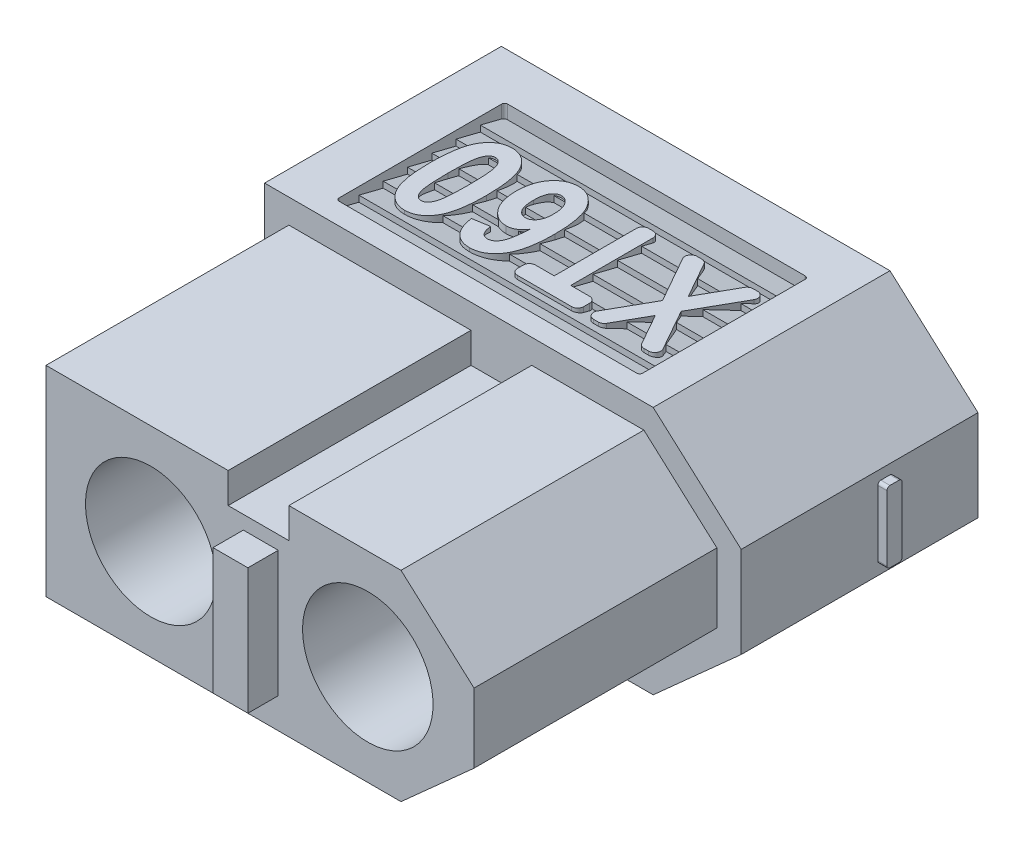
SolidWorks part; units mm, degrees
material "Náilon 101"
ref_plane "Plano frontal" through (0, 0, 0) normal (0, 0, 1) x (1, 0, 0)
ref_plane "Plano superior" through (0, 0, 0) normal (0, 1, 0) x (1, 0, 0)
ref_plane "Plano direito" through (0, 0, 0) normal (1, 0, 0) x (0, 0, -1)
sketch "Esboço1" plane through (0, 0, 0) normal (0, 0, 1) x (1, 0, 0)
  line L0 (0, 0) -> (12.8, 0)
  line L1 (12.8, 0) -> (15.7, 2.6)
  line L2 (15.7, 2.6) -> (15.7, 5.6)
  line L3 (15.7, 5.6) -> (12.8, 8.2)
  line L4 (12.8, 8.2) -> (0, 8.2)
  line L5 (0, 8.2) -> (0, 0)
  dimension "D1" = 12.8
  dimension "D2" = 3
  dimension "D3" = 15.7
  dimension "D4" = 8.2
extrude "Ressalto-extrusão1" add sketch "Esboço1" along normal blind 15.8
sketch "Esboço2" plane through (0, 0, 15.8) normal (0, 0, 1) x (1, 0, 0)
  line L0 (0.8, 7.4) -> (0.8, 0.8)
  line L1 (0.8, 0.8) -> (12.4939, 0.8)
  line L2 (12.4939, 0.8) -> (14.9, 2.9572)
  line L3 (14.9, 2.9572) -> (14.9, 5.2428)
  line L4 (14.9, 5.2428) -> (12.4939, 7.4)
  line L5 (12.4939, 7.4) -> (8.8, 7.4)
  line L6 (0, 8.2) -> (0, 0)
  line L7 (0, 0) -> (12.8, 0)
  line L8 (12.8, 0) -> (15.7, 2.6)
  line L9 (15.7, 2.6) -> (15.7, 5.6)
  line L10 (15.7, 5.6) -> (12.8, 8.2)
  line L11 (12.8, 8.2) -> (0, 8.2)
  line L12 (0, 8.2) -> (0, 0)
  line L13 (0, 0) -> (12.8, 0)
  line L14 (12.8, 0) -> (15.7, 2.6)
  line L15 (15.7, 2.6) -> (15.7, 5.6)
  line L16 (15.7, 5.6) -> (12.8, 8.2)
  line L17 (12.8, 8.2) -> (0, 8.2)
  line L18 (6.8, 7.4) -> (0.8, 7.4)
  line L20 (6.8, 7.4) -> (6.8, 6.4)
  line L21 (6.8, 6.4) -> (8.8, 6.4)
  line L22 (8.8, 7.4) -> (8.8, 6.4)
  line L23 (12.4939, 7.4) -> (0.8, 7.4) construction
  dimension "D3" = 2
  dimension "D4" = 6
  dimension "D5" = 1
  dimension "D1" = 0
  dimension "D2" = 0.8
extrude "Corte-extrusão1" cut sketch "Esboço2" against normal blind 8
sketch "Esboço5" plane through (0, 0, 0) normal (0, 0, -1) x (-1, 0, 0)
  line L0 (-15.7, 2.6) -> (-15.7, 5.6) construction
  line L3 (0, 8.2) -> (0, 0) construction
  circle A0 centre (-11.4, 4.1) radius 3
  circle A1 centre (-4.25, 4.1) radius 3
  point P6 (-15.7, 4.1)
  point P9 (-15.7, 4.1)
  dimension "D1" = 6
  dimension "D3" = 4.25
  dimension "D2" = 4.3
extrude "Corte-extrusão3" cut sketch "Esboço5" against normal blind 2
sketch "Esboço6" plane through (0, 0, 2) normal (0, 0, -1) x (-1, 0, 0)
  circle A0 centre (-11.4, 4.1) radius 2.15
  circle A1 centre (-11.4, 4.1) radius 3 construction
  circle A2 centre (-4.25, 4.1) radius 2.15
  dimension "D1" = 4.3
  dimension "D2" = 2.85
extrude "Corte-extrusão4" cut sketch "Esboço6" against normal through all
sketch "Esboço7" plane through (0, 0, 0) normal (-1, 0, 0) x (0, 0, 1)
  line L0 (2.8, 4.35) -> (2.05, 4.35)
  line L1 (4.25, 4.35) -> (3.5, 4.35)
  line L2 (4.35, 4.25) -> (4.35, 3.95)
  line L3 (4.25, 3.85) -> (3.5, 3.85)
  line L4 (1.95, 4.25) -> (1.95, 3.95)
  line L5 (3.3, 5.3) -> (3, 5.3)
  line L6 (3.4, 5.2) -> (3.4, 4.45)
  line L7 (3.3, 2.9) -> (3, 2.9)
  line L8 (2.9, 5.2) -> (2.9, 4.45)
  line L9 (2.8, 3.85) -> (2.05, 3.85)
  line L10 (3.4, 3.75) -> (3.4, 3)
  line L11 (2.9, 3.75) -> (2.9, 3)
  line L12 (0, 8.2) -> (0, 0) construction
  arc A0 (3, 2.9) -> (2.9, 3) centre (3, 3) cw
  arc A1 (3.3, 5.3) -> (3.4, 5.2) centre (3.3, 5.2) cw
  arc A2 (3, 5.3) -> (2.9, 5.2) centre (3, 5.2) ccw
  arc A3 (2.05, 4.35) -> (1.95, 4.25) centre (2.05, 4.25) ccw
  arc A4 (2.05, 3.85) -> (1.95, 3.95) centre (2.05, 3.95) cw
  arc A5 (2.8, 3.85) -> (2.9, 3.75) centre (2.8, 3.75) cw
  arc A6 (2.8, 4.35) -> (2.9, 4.45) centre (2.8, 4.45) ccw
  arc A7 (3.5, 3.85) -> (3.4, 3.75) centre (3.5, 3.75) ccw
  arc A8 (3.4, 3) -> (3.3, 2.9) centre (3.3, 3) cw
  arc A9 (4.35, 3.95) -> (4.25, 3.85) centre (4.25, 3.95) cw
  arc A10 (4.25, 4.35) -> (4.35, 4.25) centre (4.25, 4.25) cw
  arc A11 (3.5, 4.35) -> (3.4, 4.45) centre (3.5, 4.45) cw
  point P12 (1.95, 4.1)
  point P15 (0, 4.1)
  point P28 (2.9, 3.85)
  point P33 (3.4, 3.85)
  point P38 (4.35, 3.85)
  point P41 (4.35, 4.35)
  dimension "D4" = 0.1
  dimension "D1" = 2.4
  dimension "D2" = 0.5
  dimension "D3" = 4.35
extrude "Ressalto-extrusão3" add sketch "Esboço7" along normal blind 0.3
sketch "Esboço8" plane through (15.7, 0, 0) normal (1, 0, 0) x (0, 0, -1)
  line L0 (0, 2.6) -> (0, 5.6) construction
  line L1 (-3.2, 2.925) -> (-2.9, 2.925)
  line L2 (-3.3, 3.025) -> (-3.3, 5.175)
  line L3 (-3.2, 5.275) -> (-2.9, 5.275)
  line L4 (-2.8, 3.025) -> (-2.8, 5.175)
  arc A0 (-3.3, 5.175) -> (-3.2, 5.275) centre (-3.2, 5.175) cw
  arc A1 (-2.9, 5.275) -> (-2.8, 5.175) centre (-2.9, 5.175) cw
  arc A2 (-3.2, 2.925) -> (-3.3, 3.025) centre (-3.2, 3.025) cw
  arc A3 (-2.9, 2.925) -> (-2.8, 3.025) centre (-2.9, 3.025) ccw
  point P4 (-2.8, 4.1)
  point P7 (0, 4.1)
  point P10 (-3.3, 5.275)
  point P13 (-2.8, 5.275)
  point P18 (-2.8, 2.925)
  dimension "D4" = 0.1
  dimension "D1" = 2.35
  dimension "D2" = 0.5
  dimension "D3" = 3.3
extrude "Ressalto-extrusão4" add sketch "Esboço8" along normal blind 0.3
sketch "Esboço9" plane through (0, 0, 0) normal (0, -1, 0) x (1, 0, 0)
  line L0 (12.8, 7.8) -> (12.8, 0) construction
  line L1 (1.75, 7.0931) -> (11.55, 7.0931)
  line L2 (1.65, 6.9931) -> (1.65, 1.6431)
  line L3 (1.75, 1.5431) -> (11.55, 1.5431)
  line L4 (11.65, 6.9931) -> (11.65, 1.6431)
  arc A0 (1.65, 1.6431) -> (1.75, 1.5431) centre (1.75, 1.6431) ccw
  arc A1 (11.55, 1.5431) -> (11.65, 1.6431) centre (11.55, 1.6431) ccw
  arc A2 (11.55, 7.0931) -> (11.65, 6.9931) centre (11.55, 6.9931) cw
  arc A3 (1.75, 7.0931) -> (1.65, 6.9931) centre (1.75, 6.9931) ccw
  dimension "D1" = 0.1
  dimension "D2" = 1.15
  dimension "D3" = 10
  dimension "D4" = 5.55
extrude "Corte-extrusão5" cut sketch "Esboço9" against normal blind 0.75
sketch "Esboço10" plane through (1.65, 0, 0) normal (1, 0, 0) x (0, 0, -1)
  line L0 (-6.9931, 0.75) -> (-1.6431, 0.75) construction
  line L1 (-1.5431, 0.75) -> (-1.5431, 0) construction
  line L2 (-3.1431, 0.25) -> (-2.3431, 0.45)
  line L3 (-2.3431, 0.45) -> (-2.3431, 0.25)
  line L5 (-3.1431, 0.45) -> (-3.1431, 0.25)
  line L6 (-2.3431, 0.45) -> (-2.3431, 0.25)
  line L7 (-3.9431, 0.25) -> (-3.1431, 0.45)
  line L8 (-3.9431, 0.45) -> (-3.9431, 0.25)
  line L9 (-4.7431, 0.25) -> (-3.9431, 0.45)
  line L10 (-4.7431, 0.45) -> (-4.7431, 0.25)
  line L11 (-5.5431, 0.25) -> (-4.7431, 0.45)
  line L12 (-5.5431, 0.45) -> (-5.5431, 0.25)
  line L13 (-6.3431, 0.25) -> (-5.5431, 0.45)
  line L14 (-6.3431, 0.45) -> (-6.3431, 0.25)
  line L15 (-7.1431, 0.25) -> (-6.3431, 0.45)
  line L16 (-7.1431, 0.45) -> (-7.1431, 0.25)
  line L17 (-7.1431, 0.45) -> (-7.1431, 0.75)
  line L19 (-2.3431, 0.25) -> (-1.5431, 0.45)
  line L20 (-7.1431, 0.75) -> (-1.5431, 0.75)
  line L21 (-1.5431, 0.45) -> (-1.5431, 0.75)
  line L31 (-2.3431, 0.25) -> (-1.5431, 0.45)
  dimension "D1" = 0.8
  dimension "D2" = 0.2
  dimension "D3" = 0.3
  dimension "D4" = 7
extrude "Ressalto-extrusão7" add sketch "Esboço10" along normal up to surface (10 mm away) up to face at (11.65, 0.375, 4.3181)
ref_plane "Plano1" through (0, 4.1, 0) normal (0, 1, 0) x (1, 0, 0)
mirror "Espelhar1" about plane through (0, 4.1, 0) normal (0, 1, 0) of "Corte-extrusão5", "Ressalto-extrusão7"
ref_plane "Plano2" through (0, 0.5, 0) normal (0, -1, 0) x (-1, 0, 0)
sketch "Esboço11" plane through (0, 0.5, 0) normal (0, -1, 0) x (-1, 0, 0)
  line L0 (-11.65, -5.5431) -> (-1.65, -5.5431) construction
  line L1 (-2.5942, -5.5431) -> (-2.8167, -5.5431)
  line L2 (-2.4442, -5.6931) -> (-2.4442, -5.9931)
  line L3 (-2.5942, -6.1431) -> (-4.2856, -6.1431)
  line L4 (-4.4356, -5.6931) -> (-4.4356, -5.9931)
  line L5 (-2.9644, -5.3671) -> (-2.4752, -2.5928)
  line L6 (-2.6229, -2.4167) -> (-2.9229, -2.4167)
  line L7 (-3.0707, -2.5407) -> (-3.5782, -5.4192)
  line L8 (-7.3128, -6.1431) -> (-5.9872, -6.1431)
  line L9 (-5.8573, -6.0681) -> (-5.8287, -6.0186)
  line L10 (-5.5911, -5.3659) -> (-5.1507, -2.8681)
  line L11 (-5.6643, -2.4167) -> (-6.7472, -2.4167)
  line L12 (-6.8771, -2.4917) -> (-7.2464, -3.1314)
  line L13 (-7.2611, -3.163) -> (-7.4867, -3.7828)
  line L14 (-7.4957, -3.8165) -> (-7.6002, -4.4092)
  line L15 (-7.4525, -4.5852) -> (-6.8146, -4.5852)
  line L16 (-6.6646, -4.4352) -> (-6.6646, -4.1352)
  line L17 (-6.9804, -3.6253) -> (-6.8543, -3.899)
  line L20 (-6.6242, -3.0167) -> (-5.9053, -3.0167)
  line L21 (-5.8069, -3.1341) -> (-6.2098, -5.4192)
  line L22 (-6.9749, -3.4469) -> (-6.8004, -3.1221)
  line L23 (-6.3575, -5.5431) -> (-7.0764, -5.5431)
  line L24 (-7.1749, -5.4258) -> (-7.1512, -5.2917)
  line L25 (-4.4356, -6.1431) -> (-5.9006, -6.1431) construction
  line L26 (-7.2989, -5.1157) -> (-7.599, -5.1157)
  line L27 (-7.7467, -5.2396) -> (-7.8264, -5.6918)
  line L28 (-7.7689, -5.8377) -> (-7.403, -6.113)
  line L29 (-8.9766, -6.1431) -> (-9.2766, -6.1431)
  line L30 (-9.4266, -5.9918) -> (-9.4198, -5.2132)
  line L31 (-9.5094, -5.1823) -> (-10.2035, -6.0846)
  line L32 (-10.3224, -6.1431) -> (-10.6224, -6.1431)
  line L33 (-10.7413, -5.9017) -> (-9.4154, -4.178)
  line L34 (-9.4154, -4.178) -> (-9.1267, -2.5407)
  line L35 (-8.979, -2.4167) -> (-8.679, -2.4167)
  line L36 (-8.5313, -2.5928) -> (-8.8108, -4.178)
  line L37 (-8.8108, -4.178) -> (-8.8266, -5.9944)
  line L38 (-3.7259, -5.5431) -> (-4.2856, -5.5431)
  line L39 (-5.2082, -2.7221) -> (-5.5741, -2.4469)
  line L40 (-7.3629, -6.1431) -> (-8.8279, -6.1431) construction
  line L41 (-11.55, -7.0931) -> (-1.75, -7.0931) construction
  arc A0 (-6.2098, -5.4192) -> (-6.3575, -5.5431) centre (-6.3575, -5.3931) cw
  arc A1 (-7.2464, -3.1314) -> (-7.2611, -3.163) centre (-7.0732, -3.2314) ccw
  arc A2 (-7.4957, -3.8165) -> (-7.4867, -3.7828) centre (-7.2988, -3.8512) cw
  arc A3 (-6.8543, -3.899) -> (-6.7538, -3.9981) centre (-6.6727, -3.8153) ccw
  arc A4 (-6.6646, -4.1352) -> (-6.7538, -3.9981) centre (-6.8146, -4.1352) ccw
  arc A5 (-6.8146, -4.5852) -> (-6.6646, -4.4352) centre (-6.8146, -4.4352) ccw
  arc A6 (-7.6002, -4.4092) -> (-7.4525, -4.5852) centre (-7.4525, -4.4352) ccw
  arc A7 (-7.1512, -5.2917) -> (-7.2989, -5.1157) centre (-7.2989, -5.2657) ccw
  arc A8 (-7.599, -5.1157) -> (-7.7467, -5.2396) centre (-7.599, -5.2657) ccw
  arc A9 (-10.6224, -6.1431) -> (-10.7413, -5.9017) centre (-10.6224, -5.9931) cw
  arc A10 (-10.2035, -6.0846) -> (-10.3224, -6.1431) centre (-10.3224, -5.9931) cw
  arc A11 (-9.2766, -6.1431) -> (-9.4266, -5.9918) centre (-9.2766, -5.9931) cw
  arc A12 (-8.9766, -6.1431) -> (-8.8266, -5.9944) centre (-8.9766, -5.9931) ccw
  arc A13 (-8.679, -2.4167) -> (-8.5313, -2.5928) centre (-8.679, -2.5667) cw
  arc A14 (-9.1267, -2.5407) -> (-8.979, -2.4167) centre (-8.979, -2.5667) cw
  arc A15 (-2.4752, -2.5928) -> (-2.6229, -2.4167) centre (-2.6229, -2.5667) ccw
  arc A16 (-2.9229, -2.4167) -> (-3.0707, -2.5407) centre (-2.9229, -2.5667) ccw
  arc A17 (-2.9644, -5.3671) -> (-2.8167, -5.5431) centre (-2.8167, -5.3931) ccw
  arc A18 (-3.5782, -5.4192) -> (-3.7259, -5.5431) centre (-3.7259, -5.3931) cw
  arc A19 (-4.2856, -5.5431) -> (-4.4356, -5.6931) centre (-4.2856, -5.6931) ccw
  arc A20 (-4.2856, -6.1431) -> (-4.4356, -5.9931) centre (-4.2856, -5.9931) cw
  arc A21 (-2.5942, -5.5431) -> (-2.4442, -5.6931) centre (-2.5942, -5.6931) cw
  arc A22 (-2.4442, -5.9931) -> (-2.5942, -6.1431) centre (-2.5942, -5.9931) cw
  arc A23 (-7.0764, -5.5431) -> (-7.1749, -5.4258) centre (-7.0764, -5.4431) cw
  arc A24 (-5.9053, -3.0167) -> (-5.8069, -3.1341) centre (-5.9053, -3.1167) cw
  arc A25 (-6.9804, -3.6253) -> (-6.9749, -3.4469) centre (-6.7988, -3.5416) cw
  arc A26 (-5.8287, -6.0186) -> (-5.5911, -5.3659) centre (-7.5607, -5.0186) ccw
  arc A27 (-6.7472, -2.4167) -> (-6.8771, -2.4917) centre (-6.7472, -2.5667) ccw
  arc A28 (-5.5741, -2.4469) -> (-5.6643, -2.4167) centre (-5.6643, -2.5667) ccw
  arc A29 (-5.2082, -2.7221) -> (-5.1507, -2.8681) centre (-5.2984, -2.842) cw
  arc A30 (-5.9872, -6.1431) -> (-5.8573, -6.0681) centre (-5.9872, -5.9931) ccw
  arc A31 (-7.8264, -5.6918) -> (-7.7689, -5.8377) centre (-7.6787, -5.7178) ccw
  arc A32 (-7.3128, -6.1431) -> (-7.403, -6.113) centre (-7.3128, -5.9931) cw
  arc A33 (-9.4198, -5.2132) -> (-9.5094, -5.1823) centre (-9.4698, -5.2128) ccw
  arc A34 (-6.6242, -3.0167) -> (-6.8004, -3.1221) centre (-6.6242, -3.2167) ccw
  point P14 (-6.65, -6.1431)
  point P46 (-6.65, -7.0931)
  point P50 (-6.2316, -5.5431)
  point P67 (-7.7248, -5.1157)
  point P83 (-2.4442, -2.4167)
  point P88 (-2.9954, -5.5431)
  point P91 (-3.6001, -5.5431)
  point P94 (-4.4356, -5.5431)
  point P100 (-2.4442, -5.5431)
  point P103 (-2.4442, -6.1431)
  point P106 (-7.1955, -5.5431)
  point P114 (-5.6524, -5.7132)
  point P119 (-5.6142, -2.4167)
  point P122 (-5.1347, -2.7775)
  dimension "D13" = 0.15
  dimension "D14" = 0.1
  dimension "D16" = 0.15
  dimension "D17" = 0.05
  dimension "D2" = 0.2
  dimension "D4" = 0.2
  dimension "D3" = 0.6
  dimension "D5" = 80
  dimension "D6" = 80
  dimension "D7" = 80
  dimension "D8" = 0.6
  dimension "D9" = 0.6
  dimension "D10" = 60
  dimension "D11" = 0.6
extrude "Ressalto-extrusão8" add sketch "Esboço11" along normal blind 0.3
ref_plane "Plano3" through (0, 7.7, 0) normal (0, 1, 0) x (1, 0, 0)
sketch "Esboço12" plane through (0, 7.7, 0) normal (0, 1, 0) x (1, 0, 0)
  line L0 (11.0942, -7.0931) -> (11.0942, -1.5431) construction
  line L1 (11.55, -7.0931) -> (1.75, -7.0931) construction
  line L3 (11.3535, -6.0681) -> (11.3535, -2.5681) construction
  line L6 (11.3535, -2.5681) -> (1.9746, -2.5681) construction
  line L7 (11.185, -2.8665) -> (10.3201, -4.3984)
  line L8 (10.3201, -4.3984) -> (11.0942, -5.7698)
  line L9 (10.92, -6.0681) -> (10.7649, -6.0681)
  line L10 (10.5908, -5.9665) -> (10.0126, -4.9431)
  line L11 (10.0126, -4.9431) -> (9.435, -5.9664)
  line L12 (9.2609, -6.0681) -> (9.1051, -6.0681)
  line L13 (8.931, -5.7698) -> (9.705, -4.3984)
  line L14 (9.705, -4.3984) -> (8.8401, -2.8665)
  line L15 (9.0143, -2.5681) -> (9.1699, -2.5681)
  line L16 (9.3441, -2.6698) -> (10.0126, -3.8543)
  line L17 (10.0126, -3.8543) -> (10.6817, -2.6698)
  line L18 (10.8559, -2.5681) -> (11.0109, -2.5681)
  line L19 (7.7626, -2.7681) -> (7.7626, -5.4772)
  line L20 (7.7626, -5.4772) -> (8.3808, -5.4772)
  line L21 (8.5808, -5.6772) -> (8.5808, -5.8681)
  line L22 (8.3808, -6.0681) -> (6.5989, -6.0681)
  line L23 (6.3989, -5.8681) -> (6.3989, -5.6772)
  line L24 (6.5989, -5.4772) -> (7.2171, -5.4772)
  line L25 (7.2171, -5.4772) -> (7.2171, -2.7681)
  line L26 (7.4171, -2.5681) -> (7.5626, -2.5681)
  line L27 (4.2171, -5.2045) -> (4.7626, -5.1136)
  line L28 (11.55, -1.5431) -> (1.75, -1.5431) construction
  arc A0 (7.2171, -2.7681) -> (7.4171, -2.5681) centre (7.4171, -2.7681) cw
  arc A1 (7.7626, -2.7681) -> (7.5626, -2.5681) centre (7.5626, -2.7681) ccw
  arc A2 (6.3989, -5.6772) -> (6.5989, -5.4772) centre (6.5989, -5.6772) cw
  arc A3 (6.5989, -6.0681) -> (6.3989, -5.8681) centre (6.5989, -5.8681) cw
  arc A4 (8.5808, -5.8681) -> (8.3808, -6.0681) centre (8.3808, -5.8681) cw
  arc A5 (8.3808, -5.4772) -> (8.5808, -5.6772) centre (8.3808, -5.6772) cw
  arc A6 (11.185, -2.8665) -> (11.0109, -2.5681) centre (11.0109, -2.7681) ccw
  arc A7 (10.6817, -2.6698) -> (10.8559, -2.5681) centre (10.8559, -2.7681) cw
  arc A8 (9.1699, -2.5681) -> (9.3441, -2.6698) centre (9.1699, -2.7681) cw
  arc A9 (8.8401, -2.8665) -> (9.0143, -2.5681) centre (9.0143, -2.7681) cw
  arc A10 (9.1051, -6.0681) -> (8.931, -5.7698) centre (9.1051, -5.8681) cw
  arc A11 (9.435, -5.9664) -> (9.2609, -6.0681) centre (9.2609, -5.8681) cw
  arc A12 (10.7649, -6.0681) -> (10.5908, -5.9665) centre (10.7649, -5.8681) cw
  arc A13 (11.0942, -5.7698) -> (10.92, -6.0681) centre (10.92, -5.8681) cw
  spline S0 degree 3 poles (4.7626, -5.1136) (4.7682, -5.1739) (4.7813, -5.2594) (4.8192, -5.3612) (4.8534, -5.4198) (4.8944, -5.4666) (4.9618, -5.511) (5.022, -5.5233) (5.0623, -5.5227) knots 0 0 0 0 0.323351 0.457032 0.575726 0.682828 0.785622 1 1 1 1
  spline S1 degree 3 poles (5.0623, -5.5227) (5.09, -5.5233) (5.1312, -5.5165) (5.1832, -5.4965) (5.2201, -5.4751) (5.2548, -5.4474) (5.2873, -5.4137) (5.3188, -5.3744) (5.3485, -5.328) (5.3759, -5.2719) (5.4005, -5.2044) (5.4208, -5.1242) (5.4414, -5.0325) (5.4567, -4.9277) (5.4769, -4.7639) (5.4853, -4.6343) (5.4898, -4.544) knots 0 0 0 0 0.071106 0.106432 0.143035 0.180361 0.220458 0.263402 0.309744 0.362096 0.423824 0.494518 0.575001 0.665718 0.767055 1 1 1 1
  spline S2 degree 3 poles (5.4898, -4.544) (5.4583, -4.5903) (5.407, -4.6546) (5.3276, -4.7255) (5.2671, -4.7681) (5.2028, -4.8002) (5.1126, -4.8326) (5.0401, -4.8399) (4.992, -4.8409) knots 0 0 0 0 0.277998 0.405178 0.526602 0.643637 0.760549 1 1 1 1
  spline S3 degree 3 poles (4.992, -4.8409) (4.9384, -4.84) (4.8576, -4.8324) (4.7559, -4.798) (4.6823, -4.7636) (4.6106, -4.7202) (4.5426, -4.6656) (4.4769, -4.602) (4.4148, -4.529) (4.3577, -4.4481) (4.3074, -4.36) (4.2661, -4.2652) (4.2305, -4.1646) (4.205, -4.0571) (4.1787, -3.9021) (4.1709, -3.7817) (4.1717, -3.6995) knots 0 0 0 0 0.103373 0.154207 0.205955 0.259297 0.315055 0.373347 0.435039 0.499095 0.563542 0.6298 0.697776 0.768574 0.842016 1 1 1 1
  spline S4 degree 3 poles (4.1717, -3.6995) (4.1719, -3.6124) (4.1791, -3.4851) (4.2059, -3.3214) (4.2344, -3.2096) (4.2696, -3.1044) (4.3147, -3.0075) (4.3663, -2.9169) (4.427, -2.8357) (4.4929, -2.7625) (4.5632, -2.698) (4.638, -2.6441) (4.7161, -2.5992) (4.7984, -2.5649) (4.9149, -2.5326) (5.0059, -2.5223) (5.0673, -2.5227) knots 0 0 0 0 0.157847 0.230497 0.300424 0.366636 0.431332 0.493809 0.555163 0.614703 0.672107 0.727719 0.78152 0.834986 0.88891 1 1 1 1
  spline S5 degree 3 poles (5.0673, -2.5227) (5.1348, -2.5224) (5.235, -2.5352) (5.3621, -2.5775) (5.4516, -2.6225) (5.5367, -2.6804) (5.6167, -2.7511) (5.6923, -2.8344) (5.764, -2.9301) (5.8292, -3.0408) (5.8839, -3.1688) (5.9316, -3.3125) (5.969, -3.4733) (5.9997, -3.6502) (6.0283, -3.9192) (6.0353, -4.1298) (6.0353, -4.2755) knots 0 0 0 0 0.090693 0.134685 0.17953 0.224913 0.272738 0.32276 0.375986 0.433204 0.49507 0.562819 0.636478 0.716918 0.804031 1 1 1 1
  spline S6 degree 3 poles (6.0353, -4.2755) (6.0353, -4.4236) (6.0286, -4.6379) (5.9972, -4.9112) (5.9666, -5.0917) (5.9263, -5.2555) (5.8779, -5.4031) (5.8201, -5.5343) (5.7518, -5.6479) (5.6774, -5.7469) (5.5976, -5.8325) (5.5132, -5.906) (5.4224, -5.9645) (5.3276, -6.0115) (5.1918, -6.0556) (5.0843, -6.0686) (5.0119, -6.0681) knots 0 0 0 0 0.192658 0.278521 0.357597 0.430563 0.497753 0.559502 0.616537 0.669747 0.720292 0.768555 0.814847 0.860431 0.905809 1 1 1 1
  spline S7 degree 3 poles (5.0119, -6.0681) (4.9619, -6.0679) (4.888, -6.0616) (4.793, -6.0396) (4.7258, -6.0161) (4.6619, -5.9851) (4.6002, -5.9489) (4.5418, -5.9054) (4.4872, -5.8546) (4.4355, -5.7981) (4.3903, -5.7331) (4.3488, -5.6621) (4.3131, -5.5835) (4.2805, -5.4988) (4.2454, -5.3724) (4.226, -5.2732) (4.2171, -5.2045) knots 0 0 0 0 0.115543 0.170649 0.225187 0.279791 0.334526 0.390474 0.447811 0.50673 0.567186 0.630471 0.696846 0.766493 0.839959 1 1 1 1
  spline S8 degree 3 poles (5.4444, -3.7215) (5.4434, -3.6718) (5.4418, -3.5989) (5.429, -3.5058) (5.4165, -3.4425) (5.399, -3.3843) (5.3797, -3.33) (5.3555, -3.2808) (5.3274, -3.2367) (5.298, -3.1971) (5.2668, -3.1628) (5.2343, -3.1343) (5.2019, -3.1095) (5.1674, -3.0908) (5.1199, -3.0739) (5.0828, -3.0683) (5.058, -3.0681) knots 0 0 0 0 0.178482 0.260709 0.336948 0.409468 0.478213 0.543503 0.605673 0.665087 0.720356 0.771459 0.82001 0.866345 0.91145 1 1 1 1
  spline S9 degree 3 poles (5.058, -3.0681) (5.0113, -3.0673) (4.9398, -3.0858) (4.8626, -3.147) (4.82, -3.1972) (4.7904, -3.2464) (4.7705, -3.2897) (4.7544, -3.3389) (4.7402, -3.3931) (4.7296, -3.4532) (4.7205, -3.5442) (4.7163, -3.6154) (4.7171, -3.6647) knots 0 0 0 0 0.182718 0.277312 0.381921 0.439334 0.501577 0.568146 0.641921 0.72105 0.806868 1 1 1 1
  spline S10 degree 3 poles (4.7171, -3.6647) (4.717, -3.7159) (4.7193, -3.7901) (4.7313, -3.8847) (4.7423, -3.9476) (4.7573, -4.005) (4.7747, -4.0573) (4.7959, -4.1039) (4.8285, -4.1562) (4.8734, -4.2114) (4.9574, -4.2751) (5.0328, -4.2967) (5.0829, -4.2954) knots 0 0 0 0 0.189208 0.273855 0.352112 0.425324 0.492836 0.555472 0.613995 0.720194 0.816437 1 1 1 1
  spline S11 degree 3 poles (5.0829, -4.2954) (5.1315, -4.2955) (5.2057, -4.2763) (5.2877, -4.2147) (5.333, -4.163) (5.3652, -4.1135) (5.3866, -4.0705) (5.4042, -4.0231) (5.4192, -3.9714) (5.4302, -3.915) (5.4422, -3.8316) (5.4445, -3.7663) (5.4444, -3.7215) knots 0 0 0 0 0.192976 0.293261 0.403879 0.464413 0.527516 0.593907 0.665362 0.741186 0.821937 1 1 1 1
  spline S12 degree 3 poles (2.8776, -6.0681) (2.8107, -6.0678) (2.7113, -6.0563) (2.586, -6.0147) (2.4983, -5.9711) (2.4159, -5.915) (2.3386, -5.8466) (2.2662, -5.766) (2.1985, -5.6725) (2.1376, -5.5631) (2.0855, -5.436) (2.0419, -5.2906) (2.0063, -5.1269) (1.978, -4.9448) (1.9513, -4.6654) (1.9446, -4.4461) (1.9444, -4.294) knots 0 0 0 0 0.08972 0.132871 0.17644 0.220536 0.26618 0.314488 0.365396 0.420661 0.481834 0.549191 0.623951 0.706175 0.796104 1 1 1 1
  spline S13 degree 3 poles (1.9444, -4.294) (1.9446, -4.1424) (1.9512, -3.9238) (1.9781, -3.6451) (2.0061, -3.4634) (2.0421, -3.2998) (2.0852, -3.1545) (2.1378, -3.0275) (2.1984, -2.9183) (2.2663, -2.8251) (2.3378, -2.744) (2.4152, -2.6758) (2.4975, -2.6199) (2.5847, -2.5759) (2.7095, -2.5348) (2.8083, -2.5226) (2.8748, -2.5227) knots 0 0 0 0 0.203744 0.29357 0.37599 0.450617 0.518438 0.579462 0.634858 0.685888 0.734097 0.77985 0.824051 0.867439 0.910692 1 1 1 1
  spline S14 degree 3 poles (2.8748, -2.5227) (2.9415, -2.5237) (3.0413, -2.5333) (3.1662, -2.5756) (3.2543, -2.618) (3.3363, -2.6745) (3.4139, -2.742) (3.4862, -2.8219) (3.5413, -2.8978) (3.5827, -2.965) (3.6116, -3.0212) (3.6385, -3.082) (3.6644, -3.1471) (3.6866, -3.2179) (3.708, -3.2929) (3.7271, -3.3725) (3.744, -3.4569) (3.76, -3.5458) (3.7721, -3.64) (3.784, -3.7384) (3.792, -3.842) (3.7994, -3.9499) (3.8057, -4.1036) (3.809, -4.221) (3.808, -4.3011) knots 0 0 0 0 0.089418 0.132451 0.175762 0.219738 0.26505 0.312991 0.363505 0.390209 0.418376 0.447842 0.479108 0.512034 0.546898 0.583358 0.621467 0.661946 0.704107 0.748387 0.794432 0.842956 0.893008 1 1 1 1
  spline S15 degree 3 poles (3.808, -4.3011) (3.8078, -4.4522) (3.8011, -4.6701) (3.7744, -4.9476) (3.7461, -5.1285) (3.7104, -5.2915) (3.6671, -5.4365) (3.6147, -5.5633) (3.554, -5.6725) (3.4861, -5.7657) (3.4146, -5.8468) (3.3372, -5.915) (3.255, -5.9709) (3.1677, -6.0149) (3.0429, -6.056) (2.9441, -6.0682) (2.8776, -6.0681) knots 0 0 0 0 0.203492 0.293171 0.375116 0.449884 0.517528 0.578668 0.634169 0.685295 0.733595 0.779434 0.823719 0.867188 0.910523 1 1 1 1
  spline S16 degree 3 poles (2.8762, -5.5227) (2.9014, -5.5225) (2.9391, -5.5157) (2.9853, -5.4936) (3.0177, -5.4696) (3.0472, -5.4386) (3.0753, -5.4017) (3.1015, -5.3582) (3.1264, -5.3061) (3.1493, -5.2412) (3.1662, -5.1592) (3.1829, -5.0598) (3.1947, -4.9418) (3.2056, -4.806) (3.2148, -4.5879) (3.2172, -4.4152) (3.2171, -4.294) knots 0 0 0 0 0.054972 0.082543 0.111449 0.142586 0.175843 0.2128 0.253578 0.301908 0.362982 0.436475 0.522453 0.622213 0.734739 1 1 1 1
  spline S17 degree 3 poles (3.2171, -4.294) (3.2172, -4.173) (3.2148, -4.0006) (3.2056, -3.7827) (3.1946, -3.6468) (3.1829, -3.5291) (3.1662, -3.4301) (3.1492, -3.3487) (3.1266, -3.2841) (3.1014, -3.2324) (3.0751, -3.189) (3.0477, -3.1515) (3.0174, -3.1212) (2.9854, -3.0972) (2.9391, -3.0752) (2.9014, -3.0683) (2.8762, -3.0681) knots 0 0 0 0 0.265262 0.378009 0.477964 0.564111 0.637236 0.697923 0.746348 0.786738 0.823768 0.857504 0.888332 0.917295 0.944921 1 1 1 1
  spline S18 degree 3 poles (2.8762, -3.0681) (2.8509, -3.0683) (2.8128, -3.0749) (2.7663, -3.0974) (2.7333, -3.1209) (2.7037, -3.1525) (2.675, -3.1892) (2.6497, -3.2336) (2.6244, -3.2852) (2.6028, -3.3503) (2.5854, -3.4315) (2.5689, -3.5305) (2.5569, -3.648) (2.5471, -3.7837) (2.5374, -4.001) (2.5353, -4.1732) (2.5353, -4.294) knots 0 0 0 0 0.055564 0.083174 0.11254 0.143719 0.17775 0.214492 0.255326 0.303553 0.364206 0.437289 0.523386 0.622727 0.735409 1 1 1 1
  spline S19 degree 3 poles (2.5353, -4.294) (2.5354, -4.4152) (2.5374, -4.5879) (2.5471, -4.8059) (2.5568, -4.9419) (2.5689, -5.0598) (2.5854, -5.1593) (2.6027, -5.241) (2.6243, -5.3063) (2.6498, -5.3579) (2.6747, -5.4022) (2.7039, -5.4384) (2.7333, -5.4699) (2.7663, -5.4934) (2.8128, -5.5158) (2.8509, -5.5225) (2.8762, -5.5227) knots 0 0 0 0 0.265055 0.377494 0.477137 0.563048 0.636484 0.697511 0.745634 0.78638 0.823042 0.856591 0.887703 0.917006 0.944556 1 1 1 1
  point P7 (11.0942, -4.3181)
  point P10 (11.3535, -4.3181)
  dimension "D2" = 0.2
  dimension "D1" = 3.5
extrude "Ressalto-extrusão9" add sketch "Esboço12" along normal blind 0.3
sketch "Esboço13" plane through (0, 0, 15.8) normal (0, 0, 1) x (1, 0, 0)
  line L1 (7.3, 5.95) -> (8.45, 5.95)
  line L2 (7.3, 5.95) -> (7.3, 1.8)
  line L3 (7.3, 1.8) -> (8.45, 1.8)
  line L4 (8.45, 5.95) -> (8.45, 1.8)
  line L7 (14.9, 2.9572) -> (14.9, 5.2428) construction
  line L9 (0.8, 0.8) -> (12.4939, 0.8) construction
  dimension "D1" = 1.15
  dimension "D2" = 4.15
  dimension "D3" = 7.6
  dimension "D4" = 1
extrude "Ressalto-extrusão10" add sketch "Esboço13" along normal blind 1
